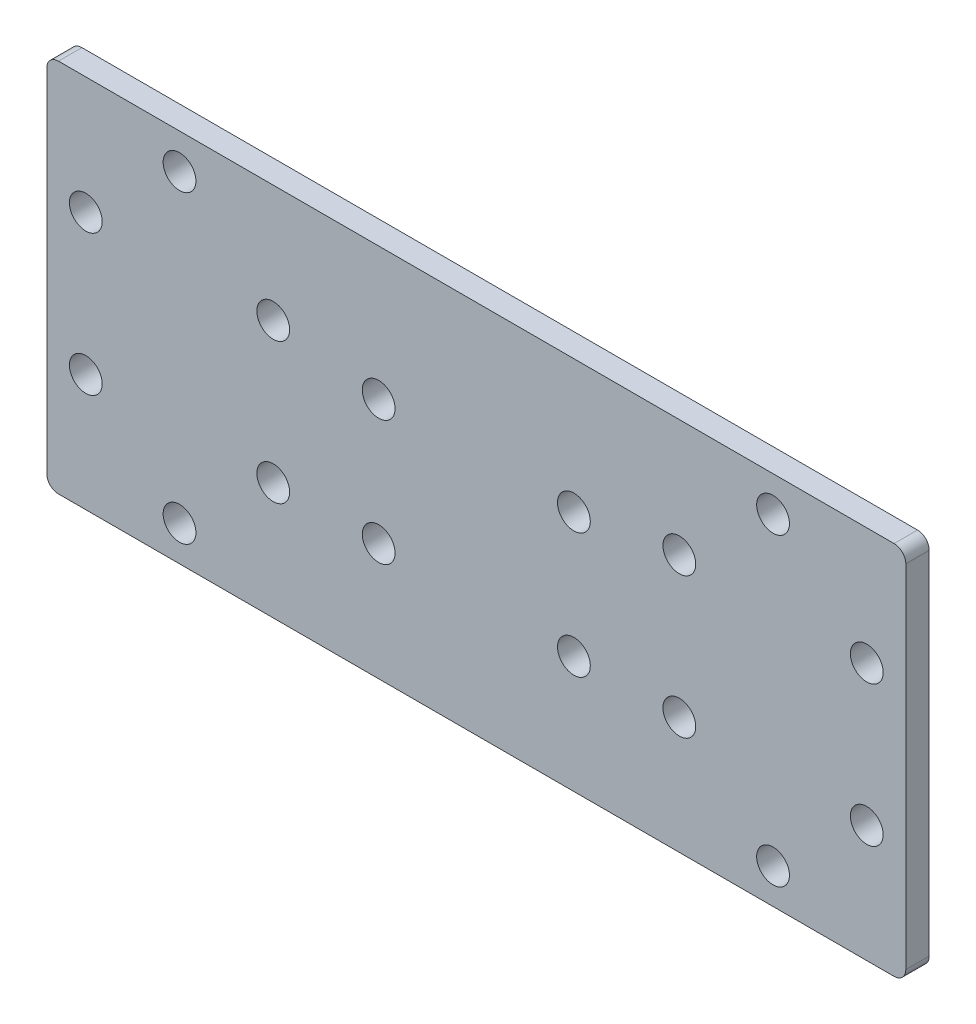
SolidWorks part; units mm, degrees
ref_plane "Front Plane" through (0, 0, 0) normal (0, 0, 1) x (1, 0, 0)
ref_plane "Top Plane" through (0, 0, 0) normal (0, 1, 0) x (1, 0, 0)
ref_plane "Right Plane" through (0, 0, 0) normal (1, 0, 0) x (0, 0, -1)
sketch "Sketch1" plane through (0, 0, 0) normal (0, 0, 1) x (1, 0, 0)
  line L0 (-55, -24) -> (55, -24)
  line L1 (-55, 24) -> (55, 24)
  line L3 (-55, -24) -> (-55, 24)
  line L4 (55, 24) -> (55, -24)
  circle A0 centre (50, 9) radius 2.1
  circle A1 centre (26, 9) radius 2.1
  circle A2 centre (50, -9) radius 2.1
  circle A3 centre (26, -9) radius 2.1
  circle A4 centre (-50, 9) radius 2.1
  circle A5 centre (-26, 9) radius 2.1
  circle A6 centre (-50, -9) radius 2.1
  circle A7 centre (-26, -9) radius 2.1
  circle A8 centre (-38, 19.5) radius 2.1
  circle A9 centre (-38, -19.5) radius 2.1
  circle A10 centre (38, 19.5) radius 2.1
  circle A11 centre (38, -19.5) radius 2.1
  circle A12 centre (12.5, -9) radius 2.1
  circle A13 centre (-12.5, -9) radius 2.1
  circle A14 centre (-12.5, 7) radius 2.1
  circle A15 centre (12.5, 7) radius 2.1
extrude "Boss-Extrude1" add sketch "Sketch1" along normal mid plane 3
fillet "Fillet1" radius 1.5 4 edges at (-55, -24, 0) (55, -24, 0) (55, 24, 0) (-55, 24, 0)
